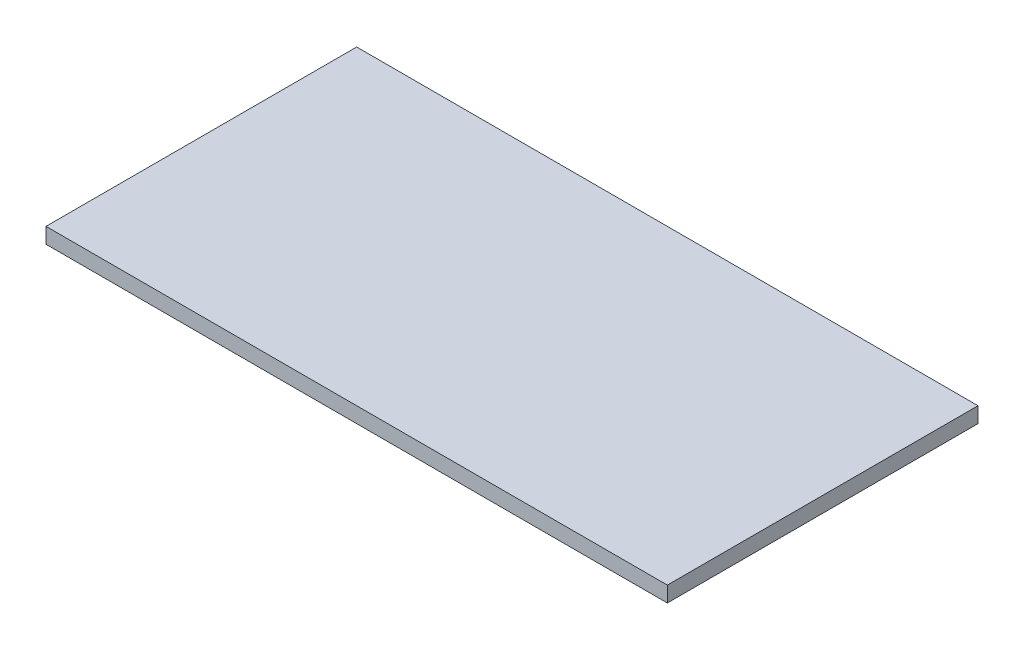
SolidWorks part; units mm, degrees
ref_plane "Front Plane" through (0, 0, 0) normal (0, 0, 1) x (1, 0, 0)
ref_plane "Top Plane" through (0, 0, 0) normal (0, 1, 0) x (1, 0, 0)
ref_plane "Right Plane" through (0, 0, 0) normal (1, 0, 0) x (0, 0, -1)
sketch "Sketch1" plane through (0, 0, 0) normal (0, 1, 0) x (1, 0, 0)
  line L1 (-768.2432, 282.7703) -> (431.7568, 282.7703)
  line L2 (-768.2432, 282.7703) -> (-768.2432, -317.2297)
  line L3 (-768.2432, -317.2297) -> (431.7568, -317.2297)
  line L4 (431.7568, 282.7703) -> (431.7568, -317.2297)
  line L5 (-768.2432, 282.7703) -> (431.7568, -317.2297) construction
  line L6 (-768.2432, -317.2297) -> (431.7568, 282.7703) construction
  point P4 (-168.2432, -17.2297)
extrude "Boss-Extrude1" add sketch "Sketch1" along normal blind 30
